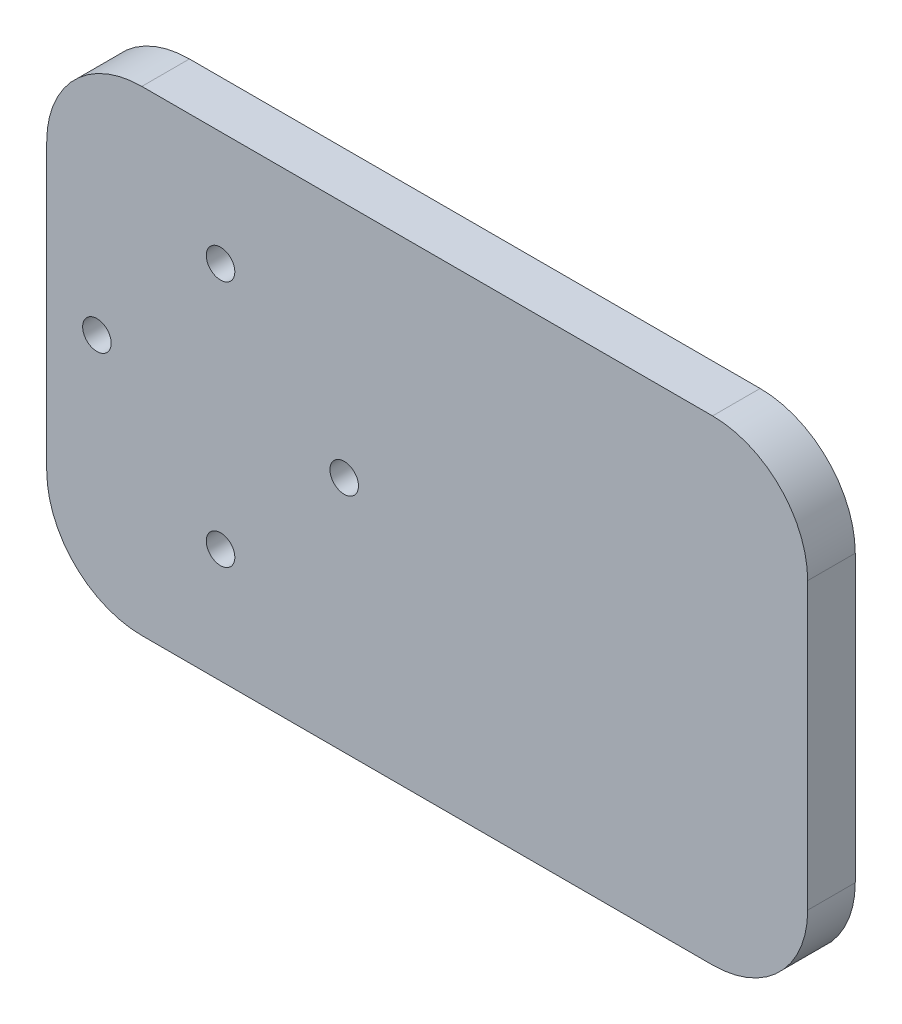
SolidWorks part; units mm, degrees
material "Acrylic (Medium-high impact)"
ref_plane "Front Plane" through (0, 0, 0) normal (0, 0, 1) x (1, 0, 0)
ref_plane "Top Plane" through (0, 0, 0) normal (0, 1, 0) x (1, 0, 0)
ref_plane "Right Plane" through (0, 0, 0) normal (1, 0, 0) x (0, 0, -1)
sketch "Sketch1" plane through (0, 0, 0) normal (0, 0, 1) x (1, 0, 0)
  line L1 (-40, 25) -> (40, 25)
  line L2 (-40, 25) -> (-40, -25)
  line L3 (-40, -25) -> (40, -25)
  line L4 (40, 25) -> (40, -25)
  line L5 (-40, 25) -> (40, -25) construction
  line L6 (-40, -25) -> (40, 25) construction
  point P0 (0, 0)
  dimension "D1" = 80
  dimension "D2" = 50
extrude "Boss-Extrude1" add sketch "Sketch1" along normal blind 5
sketch "Sketch2" plane through (0, 0, 5) normal (0, 0, 1) x (1, 0, 0)
  circle B0 centre (-21.7272, 13) radius 1.5
  circle B1 centre (-8.7272, 0) radius 1.5
  circle B2 centre (-21.7272, -13) radius 1.5
  circle B3 centre (-34.7272, 0) radius 1.5
sketch_block_instance "mounting connector-1"
sketch_block "mounting connector" parameters "D1"=3
extrude "Cut-Extrude1" cut sketch "Sketch2" against normal blind 5
sketch "Sketch3" [suppressed] plane through (0, 0, 5) normal (0, 0, 1) x (1, 0, 0)
  point P10 (-33, 0)
sketch_block_instance "Block1-1"
sketch_block "Block1" parameters "D1"=60, "D2"=30.7, "D3"=10, "D4"=3
extrude "Cut-Extrude2" [suppressed] cut sketch "Sketch3" against normal blind 5
sketch "Sketch4" [suppressed] plane through (0, 0, 0) normal (0, 0, -1) x (-1, 0, 0)
  circle A0 centre (-33.5, -8.45) radius 2
  circle A1 centre (-33.5, 8.45) radius 2
  circle A2 centre (33.5, -8.45) radius 2
  circle A3 centre (33.5, 8.45) radius 2
extrude "Cut-Extrude3" [suppressed] cut sketch "Sketch4" against normal blind 10
fillet "Fillet1" [suppressed] radius 10
fillet "Fillet2" radius 10 4 edges at (-40, -25, 2.5) (-40, 25, 2.5) (40, -25, 2.5) (40, 25, 2.5)
